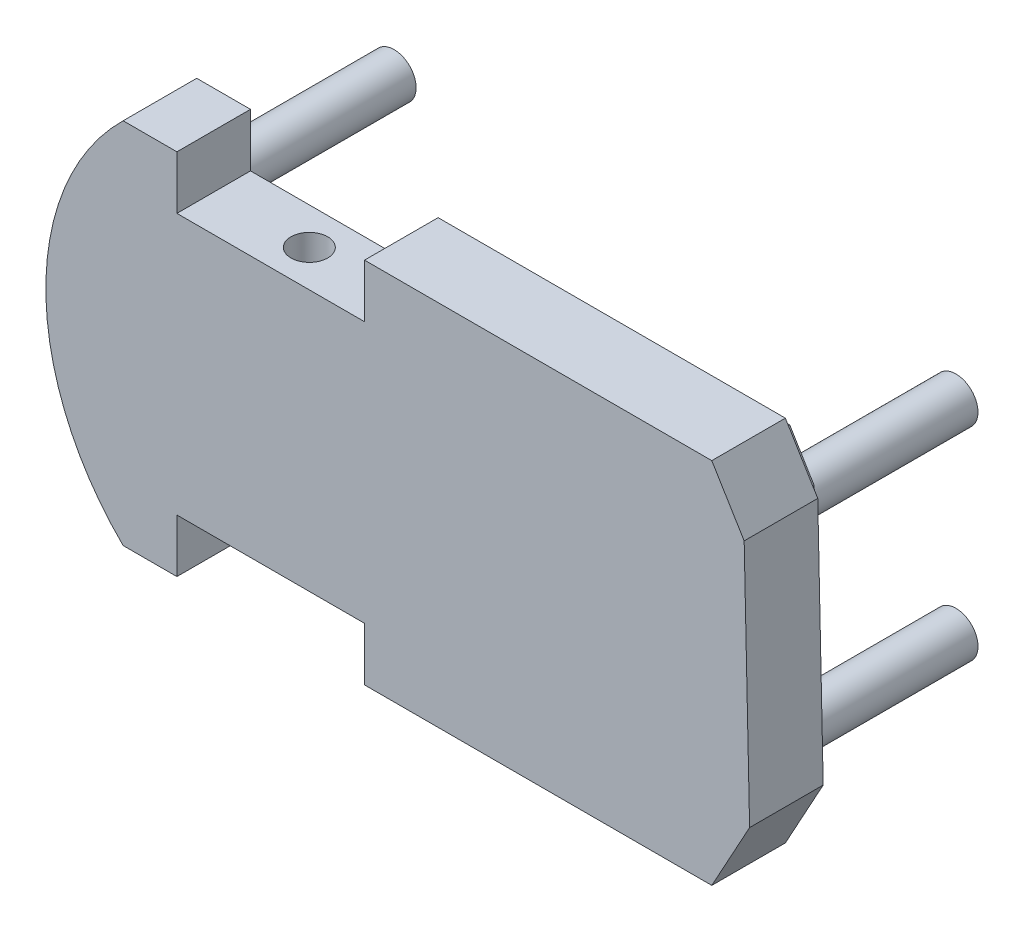
SolidWorks part; units mm, degrees
ref_plane "Front Plane" through (0, 0, 0) normal (0, 0, 1) x (1, 0, 0)
ref_plane "Top Plane" through (0, 0, 0) normal (0, 1, 0) x (1, 0, 0)
ref_plane "Right Plane" through (0, 0, 0) normal (1, 0, 0) x (0, 0, -1)
sketch "Sketch5" plane through (0, 0, 0) normal (0, 0, 1) x (1, 0, 0)
  line L0 (-1075.7074, 86.9288) -> (-1066.9035, 72.4323)
  line L1 (-1235.7074, 86.9288) -> (-1075.7074, 86.9288)
  line L2 (-1235.7074, 86.9288) -> (-1235.7074, -13.0712)
  line L3 (-1235.7074, -13.0712) -> (-1075.7074, -13.0712)
  line L4 (-1075.7074, 86.9288) -> (-1075.7074, -13.0712)
  line L5 (-1066.9035, 72.4323) -> (-1065.4231, 5.6905)
  line L6 (-1065.4231, 5.6905) -> (-1075.7074, -13.0712)
  arc A0 (-1235.7074, 86.9288) -> (-1235.7074, -13.0712) centre (-1186.7176, 36.9288) ccw
  arc A1 (2.129, 61.899) -> (11.5027, -37.6566) centre (-32.5434, 8.4153) cw
  point P16 (-1124.8683, 61.5758)
  point P17 (-1124.8683, 61.5758)
  dimension "D6" = 70
  dimension "D7" = 0
  dimension "D1" = 160
  dimension "D2" = 100
  dimension "D3" = 0
  dimension "D4" = 0
  dimension "D5" = 0
  dimension "D8" = 0
  dimension "D9" = 0
  dimension "D10" = 0
  dimension "D11" = 0
  dimension "D12" = 0
  dimension "D13" = 0
  dimension "D14" = 0
  dimension "D15" = 150
  dimension "D16" = 150
extrude "Boss-Extrude2" add sketch "Sketch5" along normal blind 20 contours L4 L1 L2 L3 | L6 L5 L0 L4 | L2 A0
sketch "Sketch6" plane through (0, 0, 20) normal (0, 0, 1) x (1, 0, 0)
  line L0 (-1329.1089, 36.9288) -> (-817.3273, 36.9288) construction
  line L1 (-1235.7074, -13.0712) -> (-1075.7074, -13.0712) construction
  line L2 (-1221.0954, -13.5712) -> (-1170.0954, -13.5712)
  line L3 (-1235.7074, 86.9288) -> (-1075.7074, 86.9288) construction
  line L4 (-1221.0954, -13.5712) -> (-1221.0954, 1.4288)
  line L5 (-1221.0954, 1.4288) -> (-1170.0954, 1.4288)
  line L6 (-1170.0954, -13.5712) -> (-1170.0954, 1.4288)
  line L7 (-1221.0954, 72.4288) -> (-1170.0954, 72.4288)
  line L8 (-1170.0954, 87.4288) -> (-1170.0954, 72.4288)
  line L9 (-1221.0954, 87.4288) -> (-1170.0954, 87.4288)
  line L10 (-1221.0954, 87.4288) -> (-1221.0954, 72.4288)
  dimension "D1" = 50
  dimension "D2" = 51
  dimension "D3" = 0.5
  dimension "D4" = 15
extrude "Cut-Extrude1" cut sketch "Sketch6" against normal through all both and the other way through all
sketch "Sketch7" plane through (0, 0, 0) normal (0, 0, -1) x (-1, 0, 0)
  line L0 (1047.1014, 36.9288) -> (1287.2995, 36.9288) construction
  line L1 (1170.0954, 86.9288) -> (1075.7074, 86.9288) construction
  line L2 (1155.7074, 109.0475) -> (1155.7074, -76.8874) construction
  circle A0 centre (1079.3449, 64.512) radius 6
  circle A1 centre (1079.3449, 9.3455) radius 6
  circle A2 centre (1232.0698, 9.3455) radius 6
  circle A3 centre (1232.0698, 64.512) radius 6
  dimension "D1" = 50
  dimension "D2" = 80
extrude "Boss-Extrude3" add sketch "Sketch7" along normal blind 50
sketch "Sketch8" plane through (0, 1.4288, 0) normal (0, -1, 0) x (1, 0, 0)
  line L0 (-1170.0954, 20) -> (-1221.0954, 20) construction
  line L1 (-1170.0954, 20) -> (-1170.0954, 0) construction
  circle A0 centre (-1195.0954, 10) radius 5
  dimension "D1" = 10
  dimension "D2" = 25
extrude "Cut-Extrude2" cut sketch "Sketch8" against normal through all both and the other way through all
sketch "Sketch9" plane through (0, 0, 0) normal (0, 0, -1) x (-1, 0, 0)
  line L39 (1165.0954, 6.4288) -> (1226.0954, 6.4288)
  line L40 (1226.0954, 6.4288) -> (1226.0954, -8.0712)
  line L41 (1226.0954, -8.0712) -> (1233.6217, -8.0712)
  line L42 (1233.6217, 81.9288) -> (1226.0954, 81.9288)
  line L43 (1226.0954, 81.9288) -> (1226.0954, 67.4288)
  line L44 (1226.0954, 67.4288) -> (1165.0954, 67.4288)
  line L45 (1165.0954, 67.4288) -> (1165.0954, 81.9288)
  line L46 (1165.0954, 81.9288) -> (1078.5207, 81.9288)
  line L47 (1078.5207, 81.9288) -> (1071.8726, 70.982)
  line L48 (1071.8726, 70.982) -> (1070.4516, 6.919)
  line L49 (1070.4516, 6.919) -> (1078.6685, -8.0712)
  line L50 (1078.6685, -8.0712) -> (1165.0954, -8.0712)
  line L51 (1165.0954, -8.0712) -> (1165.0954, 6.4288)
  line L52 (1165.0954, 6.4288) -> (1226.0954, 6.4288)
  line L53 (1226.0954, 6.4288) -> (1226.0954, -8.0712)
  line L54 (1226.0954, -8.0712) -> (1233.6217, -8.0712)
  line L55 (1233.6217, 81.9288) -> (1226.0954, 81.9288)
  line L56 (1226.0954, 81.9288) -> (1226.0954, 67.4288)
  line L57 (1226.0954, 67.4288) -> (1165.0954, 67.4288)
  line L58 (1165.0954, 67.4288) -> (1165.0954, 81.9288)
  line L59 (1165.0954, 81.9288) -> (1078.5207, 81.9288)
  line L60 (1078.5207, 81.9288) -> (1071.8726, 70.982)
  line L61 (1071.8726, 70.982) -> (1070.4516, 6.919)
  line L62 (1070.4516, 6.919) -> (1078.6685, -8.0712)
  line L63 (1078.6685, -8.0712) -> (1165.0954, -8.0712)
  line L64 (1165.0954, -8.0712) -> (1165.0954, 6.4288)
  arc A3 (1233.6217, -8.0712) -> (1233.6217, 81.9288) centre (1186.7176, 36.9288) ccw
  arc A4 (1233.6217, -8.0712) -> (1233.6217, 81.9288) centre (1186.7176, 36.9288) ccw
  dimension "D1" = 5
extrude "Boss-Extrude4" add sketch "Sketch9" along normal blind 4 contours L52 L53 L54 A4 L55 L56 L57 L58 L59 L60 L61 L62 L63 L64
sketch "Sketch10" plane through (0, 0, 0) normal (0, 0, -1) x (-1, 0, 0)
  line L26 (1170.0954, 1.4288) -> (1221.0954, 1.4288)
  line L27 (1221.0954, 1.4288) -> (1221.0954, -13.0712)
  line L28 (1221.0954, -13.0712) -> (1235.7074, -13.0712)
  line L29 (1235.7074, 86.9288) -> (1221.0954, 86.9288)
  line L30 (1221.0954, 86.9288) -> (1221.0954, 72.4288)
  line L31 (1221.0954, 72.4288) -> (1170.0954, 72.4288)
  line L32 (1170.0954, 72.4288) -> (1170.0954, 86.9288)
  line L33 (1170.0954, 86.9288) -> (1075.7074, 86.9288)
  line L34 (1075.7074, 86.9288) -> (1066.9035, 72.4323)
  line L35 (1066.9035, 72.4323) -> (1065.4231, 5.6905)
  line L36 (1065.4231, 5.6905) -> (1075.7074, -13.0712)
  line L37 (1075.7074, -13.0712) -> (1170.0954, -13.0712)
  line L38 (1170.0954, -13.0712) -> (1170.0954, 1.4288)
  line L39 (1170.0954, 1.4288) -> (1221.0954, 1.4288)
  line L40 (1221.0954, 1.4288) -> (1221.0954, -13.0712)
  line L41 (1221.0954, -13.0712) -> (1235.7074, -13.0712)
  line L42 (1235.7074, 86.9288) -> (1221.0954, 86.9288)
  line L43 (1221.0954, 86.9288) -> (1221.0954, 72.4288)
  line L44 (1221.0954, 72.4288) -> (1170.0954, 72.4288)
  line L45 (1170.0954, 72.4288) -> (1170.0954, 86.9288)
  line L46 (1170.0954, 86.9288) -> (1075.7074, 86.9288)
  line L47 (1075.7074, 86.9288) -> (1066.9035, 72.4323)
  line L48 (1066.9035, 72.4323) -> (1065.4231, 5.6905)
  line L49 (1065.4231, 5.6905) -> (1075.7074, -13.0712)
  line L50 (1075.7074, -13.0712) -> (1170.0954, -13.0712)
  line L51 (1170.0954, -13.0712) -> (1170.0954, 1.4288)
  arc A2 (1235.7074, -13.0712) -> (1235.7074, 86.9288) centre (1186.7176, 36.9288) ccw
  arc A3 (1235.7074, -13.0712) -> (1235.7074, 86.9288) centre (1186.7176, 36.9288) ccw
  dimension "D1" = 0
extrude "Boss-Extrude5" add sketch "Sketch10" against normal blind 5
